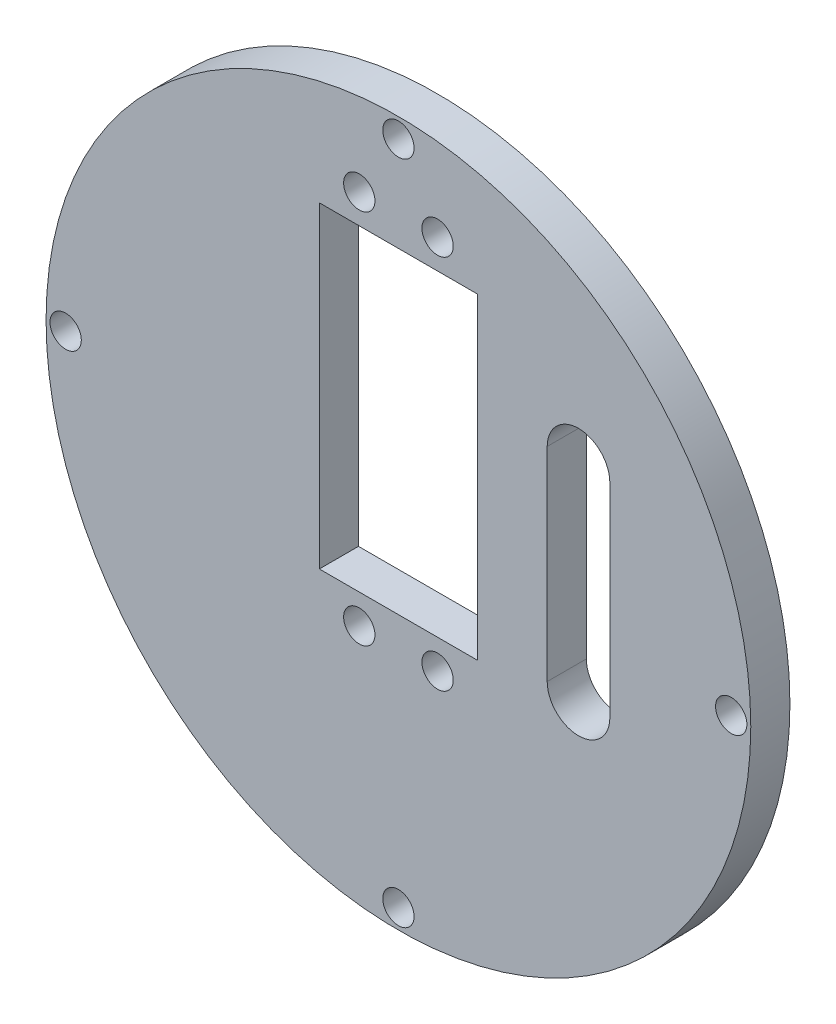
SolidWorks part; units mm, degrees
ref_plane "Front Plane" through (0, 0, 0) normal (0, 0, 1) x (1, 0, 0)
ref_plane "Top Plane" through (0, 0, 0) normal (0, 1, 0) x (1, 0, 0)
ref_plane "Right Plane" through (0, 0, 0) normal (1, 0, 0) x (0, 0, -1)
sketch "Sketch1" plane through (0, 0, 0) normal (0, 0, 1) x (1, 0, 0)
  line L0 (0, 61.1562) -> (0, -62.0155) construction
  line L1 (-10.1, 30.4) -> (10.1, 30.4)
  line L2 (-10.1, 30.4) -> (-10.1, -10.1)
  line L3 (-10.1, -10.1) -> (10.1, -10.1)
  line L4 (10.1, 30.4) -> (10.1, -10.1)
  line L5 (-10.1, 30.4) -> (10.1, -10.1) construction
  line L6 (-10.1, -10.1) -> (10.1, 30.4) construction
  line L7 (-62.9195, 0) -> (73.7046, 0) construction
  circle A0 centre (0, 0) radius 45
  circle A1 centre (0, 0) radius 1.25 construction
  circle A2 centre (-5, 34.15) radius 2
  circle A3 centre (5, 34.15) radius 2
  circle A4 centre (5, -13.85) radius 2
  circle A5 centre (-5, -13.85) radius 2
  circle A6 centre (42.5, 0) radius 2
  circle A7 centre (0, -42.5) radius 2
  circle A8 centre (-42.5, 0) radius 2
  circle A9 centre (0, 42.5) radius 2
  circle A10 centre (0, 0) radius 42.5 construction
  point P2 (0, 10.15)
  point P11 (5, -92.894)
  point P12 (5, 90.4881)
  point P13 (-96.2355, -5)
  point P14 (94.097, -5)
  point P15 (-5, -92.894)
  point P16 (-5, 90.4881)
  point P17 (-96.2355, 5)
  point P18 (94.097, 5)
  point P35 (0, 0)
  dimension "D1" = 90
  dimension "D6" = 4
  dimension "D10" = 2
  dimension "D5" = 2.5
  dimension "D14" = 4
  dimension "D13" = 85
  dimension "D2" = 20.2
  dimension "D3" = 40.5
  dimension "D7" = 3.75
  dimension "D11" = 48
  dimension "D12" = 10
  dimension "D15" = 4
  dimension "D4" = 10.1
  dimension "D8" = 5
  dimension "D9" = 2
extrude "Boss-Extrude1" add sketch "Sketch1" along normal blind 5 contours A0 A9 A8 A7 A6 A5 A4 A3 A2 L1 L4 L3 L2
sketch "Sketch2" plane through (0, 0, 0) normal (0, 0, -1) x (-1, 0, 0)
  line L0 (-23, 18) -> (-23, -8) construction
  line L1 (-19, 18) -> (-19, -8)
  line L2 (-27, 18) -> (-27, -8)
  arc A0 (-19, 18) -> (-27, 18) centre (-23, 18) ccw
  arc A1 (-27, -8) -> (-19, -8) centre (-23, -8) ccw
  circle A2 centre (0, 42.5) radius 2 construction
  point P2 (-23, 5)
  dimension "D1" = 4
  dimension "D4" = 18
  dimension "D2" = 23
  dimension "D3" = 5
extrude "Cut-Extrude1" cut sketch "Sketch2" against normal blind 10
